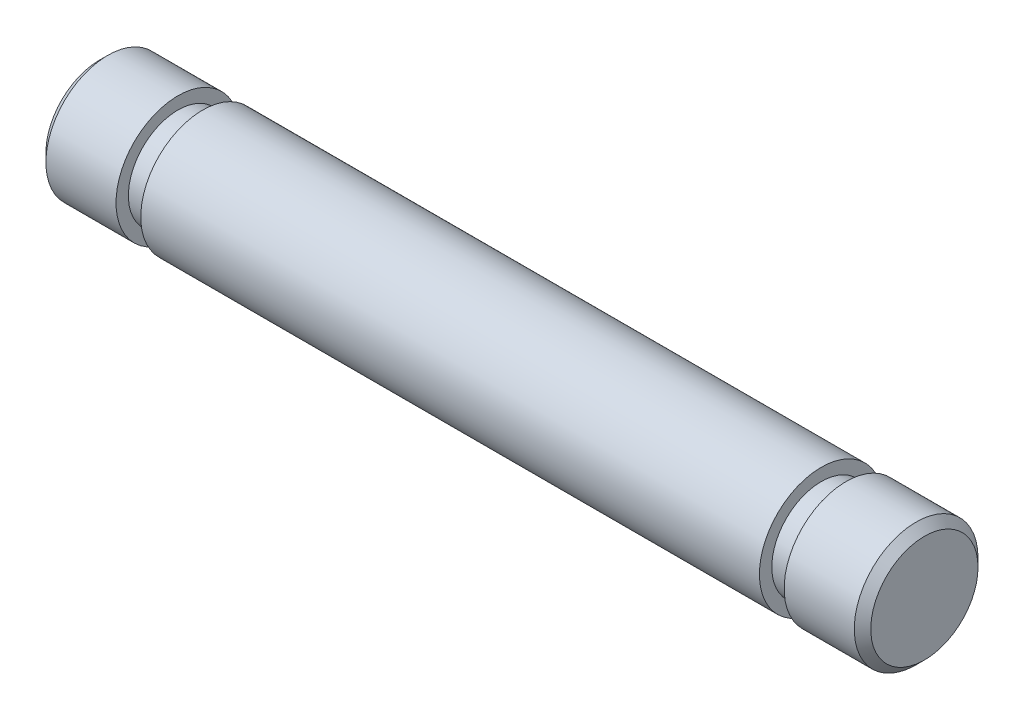
SolidWorks part; units mm, degrees
ref_plane "前视基准面" through (0, 0, 0) normal (0, 0, 1) x (1, 0, 0)
ref_plane "上视基准面" through (0, 0, 0) normal (0, 1, 0) x (1, 0, 0)
ref_plane "右视基准面" through (0, 0, 0) normal (1, 0, 0) x (0, 0, -1)
sketch "草图2" plane through (0, 0, 0) normal (1, 0, 0) x (0, 0, -1)
  circle A0 centre (0, 0) radius 1.5
  dimension "D1" = 3
extrude "凸台-拉伸1" add sketch "草图2" along normal mid plane 20
sketch "草图3" plane through (0, 0, 0) normal (1, 0, 0) x (0, 0, -1)
  circle A0 centre (0, 0) radius 1.2
  circle A1 centre (0, 0) radius 1.5 construction
  circle A2 centre (0, 0) radius 1.5
  dimension "D1" = 0.3
extrude "切除-拉伸1" cut sketch "草图3" against normal blind 0.6 from offset 7.5 offset against normal yes
mirror "镜向1" about plane through (0, 0, 0) normal (1, 0, 0) of "切除-拉伸1"
chamfer "倒角1" distance 0.2 angle 45 2 edges at (-10, 0, -1.5) (10, 0, -1.5)
